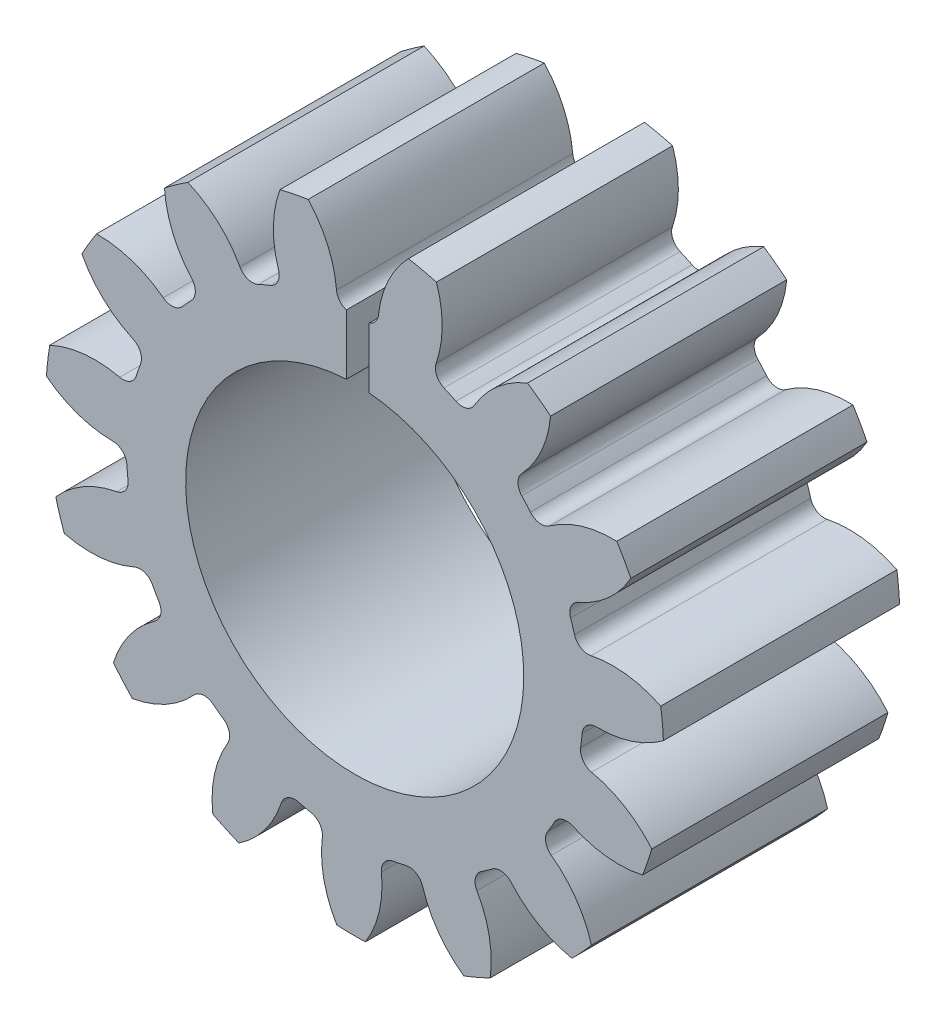
SolidWorks part; units mm, degrees
material "ABS"
ref_plane "Front" through (0, 0, 0) normal (0, 0, 1) x (1, 0, 0)
ref_plane "Top" through (0, 0, 0) normal (0, 1, 0) x (1, 0, 0)
ref_plane "Right" through (0, 0, 0) normal (1, 0, 0) x (0, 0, -1)
sketch "Sketch3" plane through (0, 0, 0) normal (0, 0, 1) x (1, 0, 0)
  circle A0 centre (0, 0) radius 21.59
  dimension "od" = 43.18
extrude "gearBody" add sketch "Sketch3" along normal blind 11
sketch "Sketch2" plane through (0, 0, 0) normal (0, 0, 1) x (1, 0, 0)
  line L0 (0, 0) -> (17.0393, 7.0579) construction
  line L1 (22.0105, -8.0941) -> (0, 0) construction
  line L2 (0, 0) -> (36.3143, 0) construction
  line L3 (19.0486, -0.229) -> (18.5878, -4.1711) construction
  line L5 (18.8182, -2.2) -> (0, 0) construction
  line L7 (0, 0) -> (18.4432, 0) construction
  arc A0 (18.4395, -0.3701) -> (18.0276, -3.8932) centre (0, 0) ccw construction
  arc A1 (21.5666, 1.0048) -> (20.7532, -5.9524) centre (0, 0) ccw construction
  arc A2 (19.0486, -0.229) -> (18.5878, -4.1711) centre (0, 0) ccw construction
  arc A3 (15.7838, -2.3046) -> (15.8898, -1.3984) centre (0, 0) ccw
  arc A4 (22.0105, -8.0941) -> (16.5506, -3.4102) centre (14.9518, -10.798) ccw
  arc A5 (22.0105, -8.0941) -> (23.2839, 2.7987) centre (0, 0) ccw
  arc A6 (23.2839, 2.7987) -> (16.8909, -0.4995) centre (17.0393, 7.0579) cw
  arc A7 (15.8898, -1.3984) -> (16.8909, -0.4995) centre (16.8715, -1.4848) cw
  arc A8 (16.5506, -3.4102) -> (15.7838, -2.3046) centre (16.759, -2.4469) cw
  arc A9 (22.9976, 9.0699) -> (16.9158, 0.7703) centre (17.0393, 7.0579) cw
  arc A10 (14.6247, -1.2871) -> (16.9158, 0.7703) centre (16.8715, -1.4848) cw
  arc A11 (14.5272, -2.1211) -> (14.6247, -1.2871) centre (0, 0) ccw
  arc A12 (16.282, -4.6514) -> (14.5272, -2.1211) centre (16.759, -2.4469) cw
  arc A13 (20.2853, -14.1302) -> (16.282, -4.6514) centre (14.9518, -10.798) ccw
  arc A14 (20.2853, -14.1302) -> (22.9976, 9.0699) centre (0, 0) ccw
  point P6 (23.2839, 2.7987)
  point P22 (22.0105, -8.0941)
  dimension "D1" = 1.27
  dimension "baseDia" = 36.8864
  dimension "od" = 43.18
  dimension "pd" = 38.1
  dimension "rd" = 31.9024
  dimension "rFillet" = 0.9855
  dimension "pointX" = 23.2839
  dimension "pointY" = 2.7987
  dimension "CTT" = 3.9421
  dimension "flankCenterAngle" = 22.5
extrude "toothCut" cut sketch "Sketch2" along normal through all contours A8 A4 A5 A6 A7 A3
pattern_circular "CirPattern1" count 15 over 360 about axis through (0, 0, 0) along (0, 0, 1) of "toothCut"
scale "Scale1" scale about centroid uniform scaling no x scale factor 0.666667 y scale factor 0.666667 z scale factor 1
sketch "hub1Dia" plane through (0, 0, 0) normal (0, 0, -1) x (-1, 0, 0)
  circle A0 centre (0, 0) radius 12.7
  dimension "hub1Dia" = 25.4
sketch "hub2Dia" plane through (0, 0, 11) normal (0, 0, 1) x (1, 0, 0)
  circle A0 centre (0, 0) radius 12.7
  dimension "hub2dia" = 25.4
sketch "boreDia" plane through (0, 0, 0) normal (0, 0, 1) x (1, 0, 0)
  circle A0 centre (0, 0) radius 7.874
  dimension "boreDia" = 15.748
extrude "bore" cut sketch "boreDia" against normal mid plane 25400
sketch "Sketch5" plane through (0, 0, 11) normal (0, 0, 1) x (1, 0, 0)
  line L1 (-0.3878, 13.0029) -> (0.6723, 13.0029)
  line L2 (-0.3878, 13.0029) -> (-0.3878, 6.4217)
  line L3 (-0.3878, 6.4217) -> (0.6723, 6.4217)
  line L4 (0.6723, 13.0029) -> (0.6723, 6.4217)
extrude "Cut-Extrude1" cut sketch "Sketch5" against normal blind 2.54
